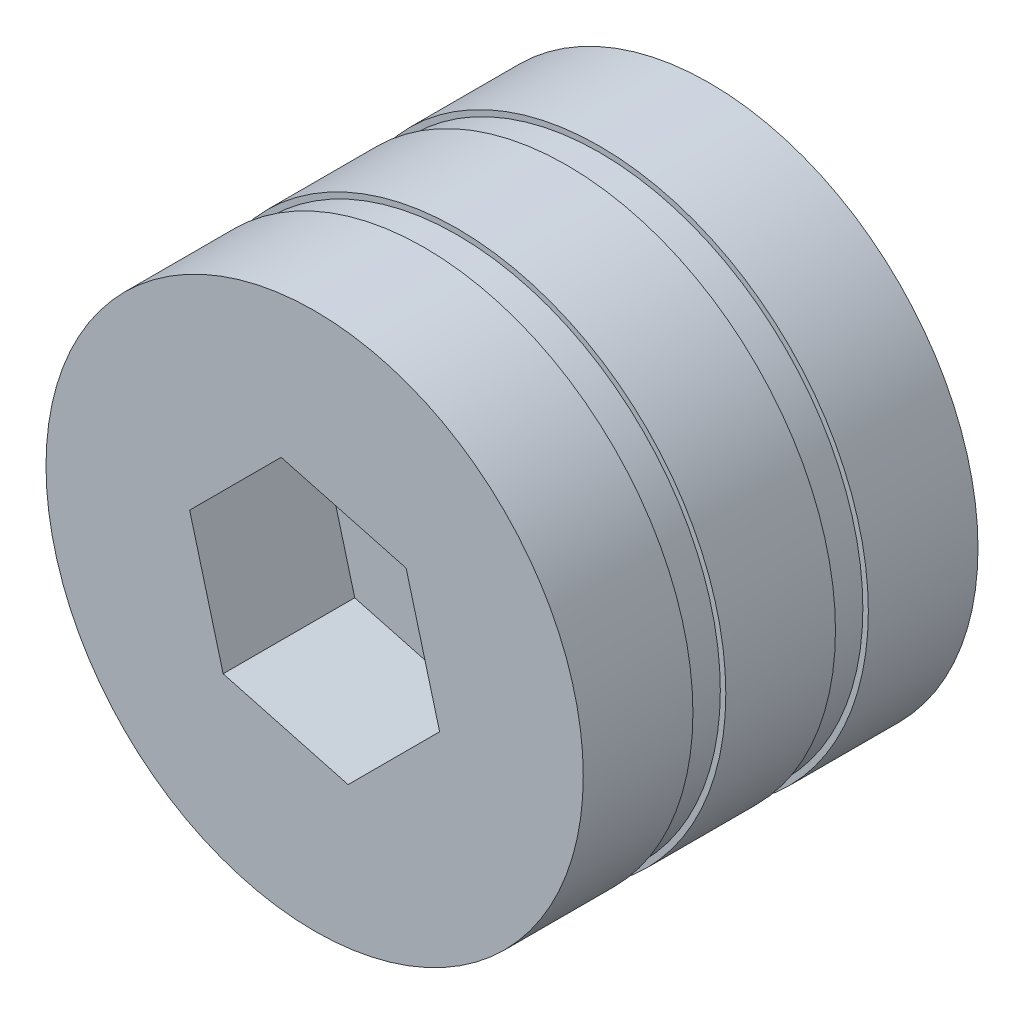
SolidWorks part; units mm, degrees
ref_plane "Front Plane" through (0, 0, 0) normal (0, 0, 1) x (1, 0, 0)
ref_plane "Top Plane" through (0, 0, 0) normal (0, 1, 0) x (1, 0, 0)
ref_plane "Right Plane" through (0, 0, 0) normal (1, 0, 0) x (0, 0, -1)
sketch "Sketch1" plane through (0, 0, 0) normal (0, 0, 1) x (1, 0, 0)
  circle A0 centre (0, 0) radius 24.5
extrude "Boss-Extrude1" add sketch "Sketch1" along normal blind 36
sketch "Sketch2" plane through (0, 0, 36) normal (0, 0, 1) x (1, 0, 0)
  line L1 (8.3439, 8.3439) -> (-3.0541, 11.3979)
  line L2 (-3.0541, 11.3979) -> (-11.3979, 3.0541)
  line L3 (-11.3979, 3.0541) -> (-8.3439, -8.3439)
  line L4 (-8.3439, -8.3439) -> (3.0541, -11.3979)
  line L5 (3.0541, -11.3979) -> (11.3979, -3.0541)
  line L6 (11.3979, -3.0541) -> (8.3439, 8.3439)
  circle A0 centre (0, 0) radius 10.2191 construction
extrude "Cut-Extrude1" cut sketch "Sketch2" against normal blind 12
sketch "Sketch3" plane through (0, 0, 36) normal (0, 0, 1) x (1, 0, 0)
  circle A0 centre (0, 0) radius 24.5
  circle A1 centre (0, 0) radius 24
extrude "Cut-Extrude2" cut sketch "Sketch3" against normal blind 3 from offset 10 offset against normal yes
sketch "Sketch4" plane through (0, 0, 36) normal (0, 0, 1) x (1, 0, 0)
  circle A0 centre (0, 0) radius 24.5
  circle A1 centre (0, 0) radius 24
extrude "Cut-Extrude3" cut sketch "Sketch4" against normal blind 3 from offset 23
